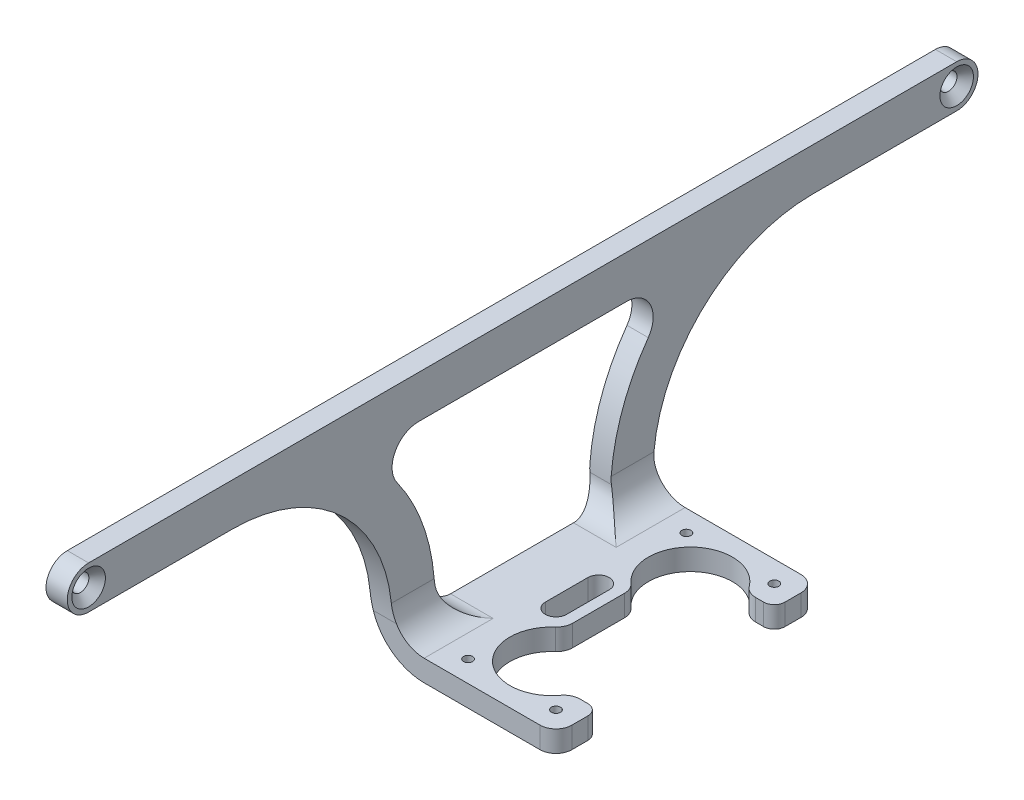
SolidWorks part; units mm, degrees
material "ABS"
ref_plane "Plan de face" through (0, 0, 0) normal (0, 0, 1) x (1, 0, 0)
ref_plane "Plan de dessus" through (0, 0, 0) normal (0, 1, 0) x (1, 0, 0)
ref_plane "Plan de droite" through (0, 0, 0) normal (1, 0, 0) x (0, 0, -1)
sketch "Esquisse1" plane through (0, 0, 0) normal (0, 0, 1) x (1, 0, 0)
  line L0 (0, 0) -> (-25, 0)
  line L1 (-35, 10) -> (-35, 45)
  line L2 (0, 4) -> (-25, 4)
  line L3 (-31, 10) -> (-31, 45)
  line L4 (0, 0) -> (0, 4)
  line L5 (-35, 45) -> (-31, 45)
  arc A2 (-25, 0) -> (-35, 10) centre (-25, 10) cw
  arc A3 (-25, 4) -> (-31, 10) centre (-25, 10) cw
  dimension "D1" = 10
  dimension "D3" = 45
  dimension "D4" = 25
  dimension "D2" = 4
extrude "Boss.-Extru.1" add sketch "Esquisse1" along normal blind 171
hole_wizard "Fraisage pour vis à tête fraisée M31" positions "Esquisse2" profile "Esquisse3" countersink size "M3" standard "ISO" end condition up to next
sketch "Esquisse2" plane through (-31, 0, 0) normal (-1, 0, 0) x (0, 0, 1)
  line L0 (0, 45) -> (0, 10) construction
  line L1 (171, 45) -> (0, 45) construction
  point P0 (4, 41)
  point P2 (167, 41)
  dimension "D1" = 163
  dimension "D2" = 4
  dimension "D3" = 4
sketch "Esquisse3" plane through (-31, 41, 4) normal (0, 1, 0) x (0, 0, -1)
  line L0 (0, 0) -> (0, 4)
  line L1 (0, 4) -> (1.6, 4)
  line L2 (1.6, 4) -> (1.6, 1.55)
  line L3 (1.6, 1.55) -> (3.15, 0)
  line L5 (3.15, 0) -> (0, 0)
  line L6 (-1.6, 1.55) -> (-3.15, 0) construction
  line L11 (0, -6.35) -> (0, 107.95) construction
  dimension "Diamètre du perçage jusqu'au prochain" = 3.2
  dimension "Profondeur du perçage jusqu'au prochain" = 4
  dimension "Diamètre du fraisage entrant" = 6.3
  dimension "Angle du fraisage entrant" = 90
hole_wizard "Dégagement M1.61" positions "Esquisse4" profile "Esquisse5" hole size "M1.6" standard "ISO" end condition up to next
sketch "Esquisse4" plane through (0, 0, 0) normal (0, -1, 0) x (-1, 0, 0)
  line L1 (20.75, -65) -> (4.25, -65)
  line L2 (20.75, -65) -> (20.75, -106)
  line L3 (20.75, -106) -> (4.25, -106)
  line L4 (4.25, -65) -> (4.25, -106)
  line L5 (20.75, -65) -> (4.25, -106) construction
  line L6 (20.75, -106) -> (4.25, -65) construction
  line L7 (25, 0) -> (0, -171) construction
  point P0 (20.75, -65)
  point P2 (20.75, -106)
  point P4 (4.25, -106)
  point P6 (4.25, -65)
  point P60 (12.5, -85.5)
  point P61 (12.5, -85.5)
  dimension "D1" = 41
  dimension "D2" = 16.5
sketch "Esquisse5" plane through (-20.75, 0, 65) normal (1, 0, 0) x (0, 0, -1)
  line L0 (0, 0) -> (0, 4)
  line L1 (0, 4) -> (0.85, 4)
  line L2 (0.85, 4) -> (0.85, 0)
  line L5 (0.85, 0) -> (0, 0)
  line L11 (0, -6.35) -> (0, 107.95) construction
  dimension "Diamètre du perçage jusqu'au prochain" = 1.7
  dimension "Profondeur du perçage jusqu'au prochain" = 4
sketch "Esquisse6" plane through (0, 0, 0) normal (0, -1, 0) x (1, 0, 0)
  line L1 (-35, 61) -> (-3.25, 61)
  line L2 (-0.25, 64) -> (-0.25, 67)
  line L3 (-3.25, 110) -> (-35, 110)
  line L5 (-35, 0) -> (0, 0)
  line L6 (0, 0) -> (0, 171)
  line L7 (0, 171) -> (-35, 171)
  line L8 (-0.25, 104) -> (-0.25, 107)
  line L9 (-3.7501, 69) -> (-2.25, 69)
  line L10 (-16.75, 80.6393) -> (-16.75, 90.3607)
  line L11 (-3.7501, 102) -> (-2.25, 102)
  line L13 (-19.25, 85.5) -> (0, 85.5) construction
  line L14 (-4.25, 106) -> (-12.5, 98.5) construction
  line L15 (-12.5, 98.5) -> (-20.75, 106) construction
  line L17 (0, 171) -> (0, 0) construction
  line L18 (-35, 171) -> (-35, 0) construction
  line L19 (-35, 110) -> (-35, 171)
  line L20 (-35, 61) -> (-35, 0)
  line L21 (-20.75, 89.5) -> (-20.75, 81.5) construction
  line L22 (-18.75, 89.5) -> (-18.75, 81.5)
  line L23 (-22.75, 89.5) -> (-22.75, 81.5)
  circle A0 centre (-4.25, 65) radius 0.85 construction
  circle A1 centre (-4.25, 106) radius 0.85 construction
  arc A2 (-0.25, 107) -> (-3.25, 110) centre (-3.25, 107) ccw
  arc A3 (-3.25, 61) -> (-0.25, 64) centre (-3.25, 64) ccw
  circle A6 centre (-20.75, 65) radius 0.85 construction
  circle A7 centre (-20.75, 106) radius 0.85 construction
  arc A12 (-6.1584, 103.211) -> (-17.7546, 92.6009) centre (-12.5, 98.5) ccw
  arc A13 (-17.7546, 78.3991) -> (-6.1584, 67.789) centre (-12.5, 72.5) ccw
  arc A14 (-6.1584, 67.789) -> (-3.7501, 69) centre (-3.7501, 66) cw
  arc A15 (-17.7546, 78.3991) -> (-16.75, 80.6393) centre (-19.75, 80.6393) ccw
  arc A16 (-3.7501, 102) -> (-6.1584, 103.211) centre (-3.7501, 105) cw
  arc A17 (-16.75, 90.3607) -> (-17.7546, 92.6009) centre (-19.75, 90.3607) ccw
  arc A18 (-2.25, 69) -> (-0.25, 67) centre (-2.25, 67) cw
  arc A19 (-2.25, 102) -> (-0.25, 104) centre (-2.25, 104) ccw
  arc A20 (-18.75, 89.5) -> (-22.75, 89.5) centre (-20.75, 89.5) ccw
  arc A21 (-22.75, 81.5) -> (-18.75, 81.5) centre (-20.75, 81.5) ccw
  point P8 (-20.75, 85.5)
  point P40 (-0.25, 102)
  dimension "D1" = 4
  dimension "D2" = 4
  dimension "D5" = 4
  dimension "D6" = 3
  dimension "D7" = 8
  dimension "D12" = 3
  dimension "D11" = 15.8
  dimension "D3" = 2
  dimension "D4" = 4
  dimension "D8" = 4
  dimension "D9" = 4
  dimension "D10" = 4
  dimension "D13" = 26
  dimension "D14" = 4
extrude "Enlèv. mat.-Extru.1" cut sketch "Esquisse6" against normal up to surface (4 mm away) up to face at (-19.9, 4, 65)
sketch "Esquisse7" plane through (-31, 0, 0) normal (1, 0, 0) x (0, 0, -1)
  line L0 (-171, 45) -> (0, 45) construction
  line L24 (0, 41) -> (0, 4)
  line L25 (-171, 41) -> (-171, 45)
  line L26 (-171, 45) -> (-167, 45)
  line L27 (-4, 45) -> (0, 45)
  line L28 (0, 45) -> (0, 41)
  line L29 (-167, 37) -> (-140, 37)
  line L30 (-110, 7) -> (-110, 4)
  line L31 (-4, 37) -> (-31, 37)
  line L32 (-61, 7) -> (-61, 4)
  line L33 (0, 4) -> (-61, 4)
  line L34 (-110, 4) -> (-171, 4)
  line L35 (-171, 4) -> (-171, 41)
  line L39 (-105.0143, 37) -> (-65.9857, 37)
  line L40 (-73.9535, 4) -> (-97.0465, 4)
  line L41 (-110, 4) -> (-61, 4) construction
  circle A8 centre (-167, 41) radius 4
  circle A15 centre (-4, 41) radius 4
  arc A16 (-31, 37) -> (-61, 7) centre (-31, 7) ccw
  arc A17 (-140, 37) -> (-110, 7) centre (-140, 7) cw
  arc A18 (-102.0411, 8.7674) -> (-109.0824, 29.093) centre (-140, 7) ccw
  arc A19 (-61.9176, 29.093) -> (-68.9589, 8.7674) centre (-31, 7) ccw
  arc A20 (-97.0465, 4) -> (-102.0411, 8.7674) centre (-97.0465, 9) cw
  arc A21 (-73.9535, 4) -> (-68.9589, 8.7674) centre (-73.9535, 9) ccw
  arc A22 (-65.9857, 37) -> (-61.9176, 29.093) centre (-65.9857, 32) cw
  arc A23 (-105.0143, 37) -> (-109.0824, 29.093) centre (-105.0143, 32) ccw
  point P20 (-110, 37)
  point P21 (-71.3522, 4.554)
  point P33 (0, 0)
  point P38 (-31, 45)
  point P39 (-98.1899, 4)
  point P41 (-140, 45)
  line M10 (0, 10) -> (0, 45)
  line M12 (0, 45) -> (-171, 45)
  line M14 (-171, 45) -> (-171, 10)
  line M15 (-171, 10) -> (0, 10)
  dimension "D1" = 30
  dimension "D2" = 5
extrude "Enlèv. mat.-Extru.2" cut sketch "Esquisse7" against normal through all and the other way through all contours A23 A18 A20 A21 A19 A22 M12 M15 | A17 L29 A8 M14 M15 | L31 A16 A15 M15 M10 | A15 M10 M12 | A8 M12 M14 | A17 L35 L34 L30 M15 | A16 L32 L33 L24 M15 | L40 A21 A19 A18 A20 M15
